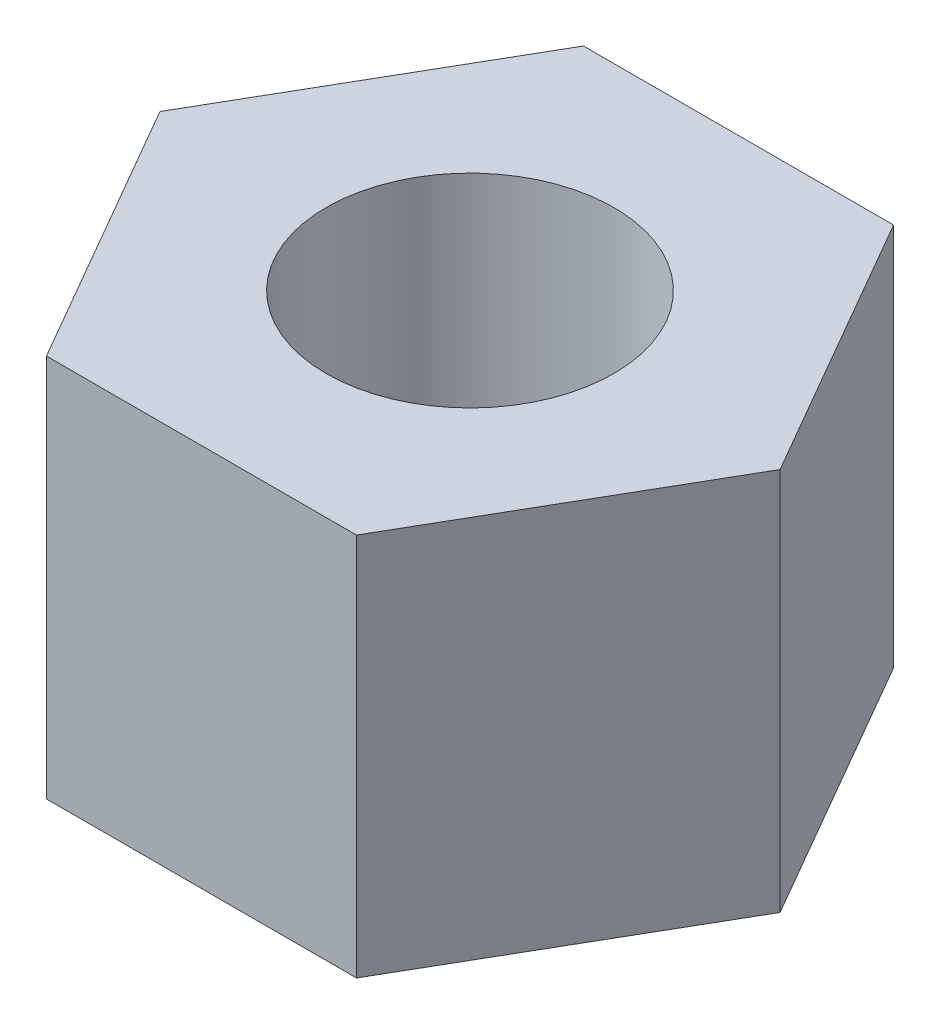
SolidWorks part; units mm, degrees
ref_plane "前视基准面" through (0, 0, 0) normal (0, 0, 1) x (1, 0, 0)
ref_plane "上视基准面" through (0, 0, 0) normal (0, 1, 0) x (1, 0, 0)
ref_plane "右视基准面" through (0, 0, 0) normal (1, 0, 0) x (0, 0, -1)
sketch "草图1" plane through (0, 0, 0) normal (0, 1, 0) x (1, 0, 0)
  line L7 (3.2332, 0) -> (1.6166, 2.8)
  line L8 (1.6166, 2.8) -> (-1.6166, 2.8)
  line L9 (-1.6166, 2.8) -> (-3.2332, 0)
  line L10 (-3.2332, 0) -> (-1.6166, -2.8)
  line L11 (-1.6166, -2.8) -> (1.6166, -2.8)
  line L12 (1.6166, -2.8) -> (3.2332, 0)
  circle A0 centre (0, 0) radius 2.8 construction
  circle A1 centre (0, 0) radius 1.5
  dimension "D2" = 3
  dimension "D1" = 5.6
extrude "凸台-拉伸1" add sketch "草图1" along normal blind 4
